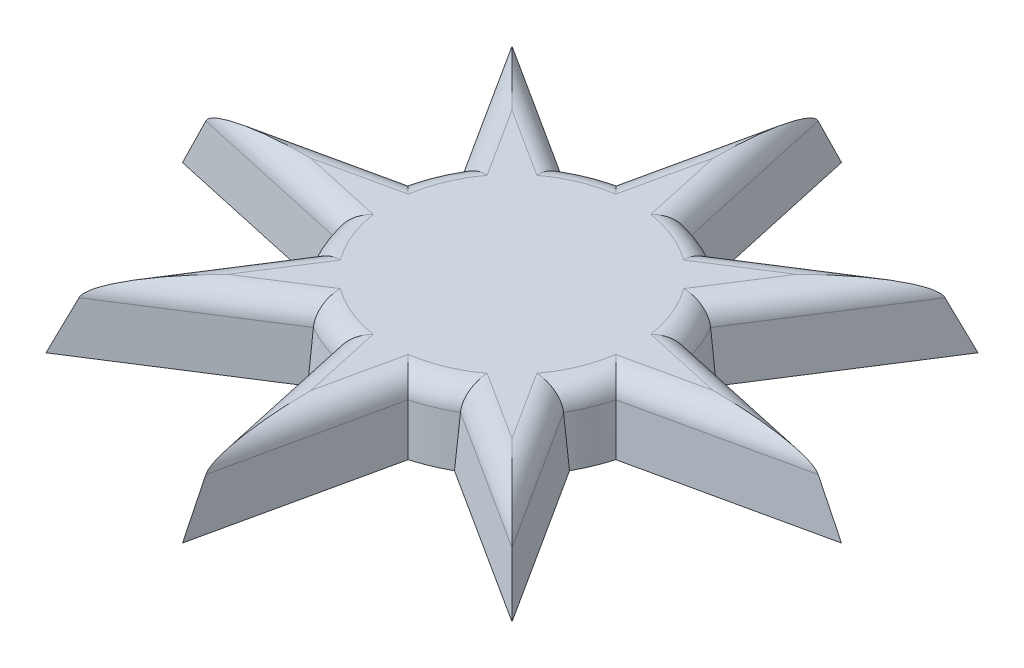
SolidWorks part; units mm, degrees
material "ABS"
ref_plane "Front Plane" through (0, 0, 0) normal (0, 0, 1) x (1, 0, 0)
ref_plane "Top Plane" through (0, 0, 0) normal (0, 1, 0) x (1, 0, 0)
ref_plane "Right Plane" through (0, 0, 0) normal (1, 0, 0) x (0, 0, -1)
sketch "Sketch1" plane through (0, 0, 0) normal (0, 1, 0) x (1, 0, 0)
  line L1 (-17.5, 17.5) -> (17.5, 17.5)
  line L2 (-17.5, 17.5) -> (-17.5, -17.5)
  line L3 (-17.5, -17.5) -> (17.5, -17.5)
  line L4 (17.5, 17.5) -> (17.5, -17.5)
  line L5 (-17.5, 17.5) -> (17.5, -17.5) construction
  line L6 (-17.5, -17.5) -> (17.5, 17.5) construction
  point P0 (0, 0)
  dimension "D1" = 35
sketch "Sketch2" plane through (0, 0, 0) normal (0, 1, 0) x (1, 0, 0)
  line L0 (0, 14.5436) -> (-1.795, 6.3768)
  line L1 (0, 14.5436) -> (0, 6.6246) construction
  line L2 (0, 14.5436) -> (1.795, 6.3768)
  line L3 (10.2839, 10.2839) -> (3.2399, 5.7783)
  line L4 (10.2839, 10.2839) -> (5.7783, 3.2399)
  line L5 (14.5436, 0) -> (6.3768, 1.795)
  line L6 (14.5436, 0) -> (6.3768, -1.795)
  line L7 (10.2839, -10.2839) -> (5.7783, -3.2399)
  line L8 (10.2839, -10.2839) -> (3.2399, -5.7783)
  line L9 (0, -14.5436) -> (1.795, -6.3768)
  line L10 (0, -14.5436) -> (-1.795, -6.3768)
  line L11 (-10.2839, -10.2839) -> (-3.2399, -5.7783)
  line L12 (-10.2839, -10.2839) -> (-5.7783, -3.2399)
  line L13 (-14.5436, 0) -> (-6.3768, -1.795)
  line L14 (-14.5436, 0) -> (-6.3768, 1.795)
  line L15 (-10.2839, 10.2839) -> (-5.7783, 3.2399)
  line L16 (-10.2839, 10.2839) -> (-3.2399, 5.7783)
  circle A0 centre (0, 0) radius 6.6246
  point P31 (0, 0)
  dimension "D1" = 8
extrude "Boss-Extrude1" add sketch "Sketch2" along normal blind 3 draft 6 contours A0 L14 L13 | A0 L16 L15 | A0 | L2 L1 A0 | A0 L4 L3 | A0 L6 L5 | A0 L8 L7 | A0 L10 L9 | A0 L12 L11 | L1 L0 A0
fillet "Fillet1" radius 1 24 edges at (-9.5981, 3, -0.7641) (-5.8291, 3, -2.4145) (-7.3272, 3, -6.2466) (-6.2466, 3, -7.3272) (-2.4145, 3, -5.8291) (-0.7641, 3, -9.5981) (0.7641, 3, -9.5981) (2.4145, 3, -5.8291) (6.2466, 3, -7.3272) (7.3272, 3, -6.2466) (5.8291, 3, -2.4145) (9.5981, 3, -0.7641) (9.5981, 3, 0.7641) (5.8291, 3, 2.4145) (7.3272, 3, 6.2466) (6.2466, 3, 7.3272) (2.4145, 3, 5.8291) (0.7641, 3, 9.5981) (-0.7641, 3, 9.5981) (-2.4145, 3, 5.8291) (-6.2466, 3, 7.3272) (-7.3272, 3, 6.2466) (-5.8291, 3, 2.4145) (-9.5981, 3, 0.7641)
